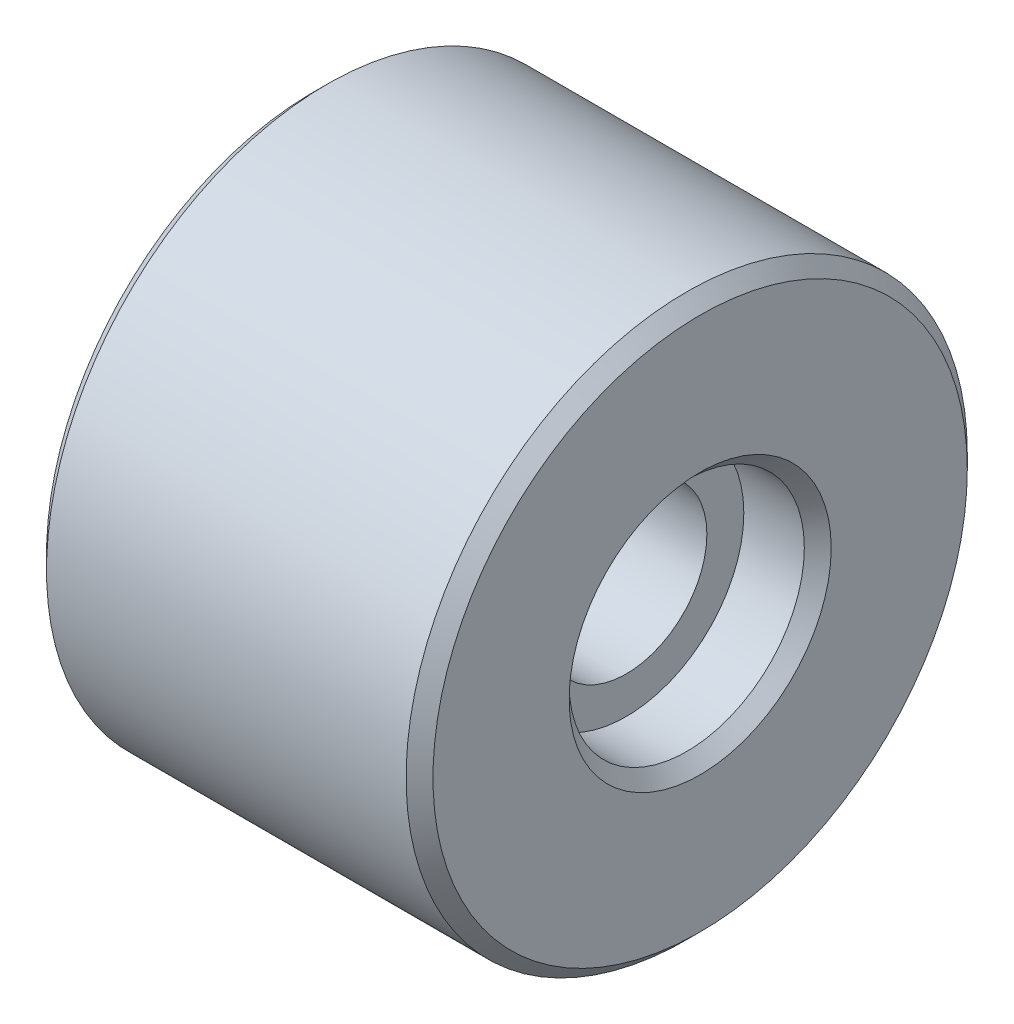
SolidWorks part; units mm, degrees
ref_plane "前视基准面" through (0, 0, 0) normal (0, 0, 1) x (1, 0, 0)
ref_plane "上视基准面" through (0, 0, 0) normal (0, 1, 0) x (1, 0, 0)
ref_plane "右视基准面" through (0, 0, 0) normal (1, 0, 0) x (0, 0, -1)
sketch "草图1" plane through (0, 0, 0) normal (1, 0, 0) x (0, 0, -1)
  circle A0 centre (0, 0) radius 8.35
  circle A1 centre (0, 0) radius 2.4
  dimension "D1" = 16.7
  dimension "D2" = 4.8
extrude "凸台-拉伸1" add sketch "草图1" along normal blind 11.5
sketch "草图2" plane through (11.5, 0, 0) normal (1, 0, 0) x (0, 0, -1)
  circle A0 centre (0, 0) radius 3.5
  dimension "D1" = 7
extrude "切除-拉伸1" cut sketch "草图2" against normal blind 2.2
chamfer "倒角1" distance 0.4 angle 45 4 edges at (0, 0, -2.4) (11.5, 0, -3.5) (0, 0, -8.35) (11.5, 0, -8.35)
